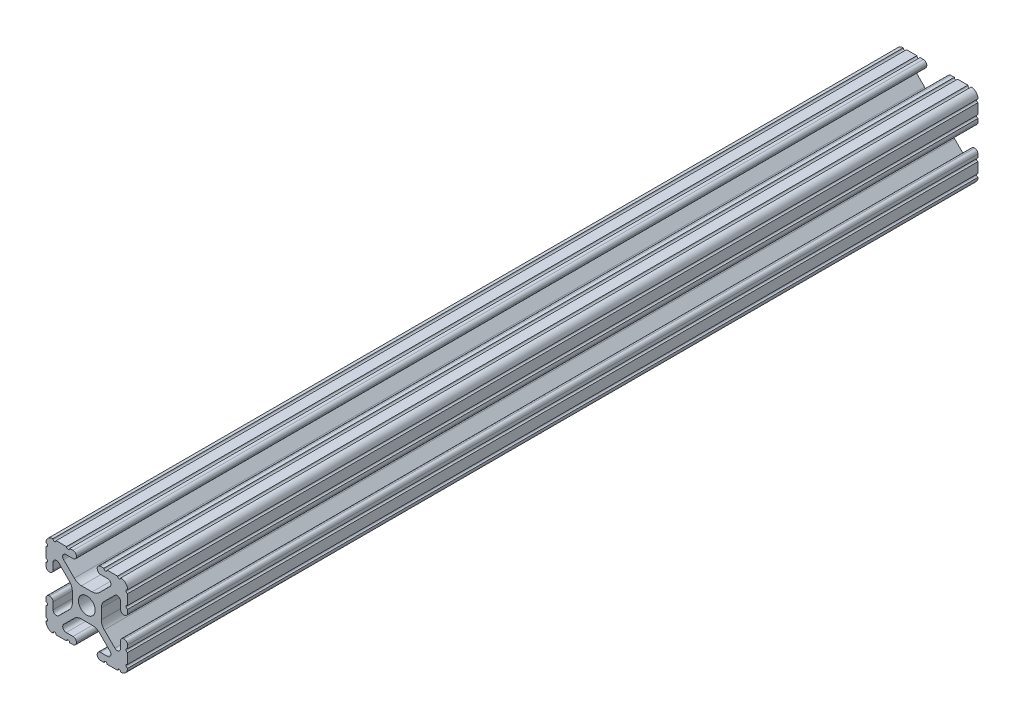
SolidWorks part; units mm, degrees
ref_plane "Front" through (0, 0, 0) normal (0, 0, 1) x (1, 0, 0)
ref_plane "Top" through (0, 0, 0) normal (0, 1, 0) x (1, 0, 0)
ref_plane "Right" through (0, 0, 0) normal (1, 0, 0) x (0, 0, -1)
sketch "Sketch1" plane through (0, 0, 0) normal (0, 0, 1) x (1, 0, 0)
  line L0 (-7.5107, 9.4563) -> (7.5107, 9.4563) construction
  line L1 (-7.4968, -9.4098) -> (7.4968, -9.4098) construction
  line L88 (-7.1797, -8.6452) -> (-3.9523, -5.4237)
  line L89 (-1.7093, -4.4958) -> (1.7093, -4.4958)
  line L90 (3.9523, -5.4237) -> (7.1797, -8.6452)
  line L91 (6.4164, -10.4902) -> (4.2875, -10.4902)
  line L92 (3.2385, -11.5392) -> (3.2385, -11.651)
  line L93 (4.2875, -12.7) -> (5.3171, -12.7)
  line L94 (6.3331, -12.7) -> (9.5504, -12.7)
  line L95 (12.7, -9.5504) -> (12.7, -6.3331)
  line L96 (12.7, -5.3171) -> (12.7, -4.2875)
  line L97 (11.651, -3.2385) -> (11.5392, -3.2385)
  line L98 (10.4902, -4.2875) -> (10.4902, -6.4021)
  line L99 (8.7371, -7.1294) -> (5.441, -3.8408)
  line L100 (4.5085, -1.5932) -> (4.5085, 1.5932)
  line L101 (5.441, 3.8408) -> (8.7371, 7.1294)
  line L102 (10.4902, 6.4021) -> (10.4902, 4.2875)
  line L103 (11.5392, 3.2385) -> (11.651, 3.2385)
  line L104 (12.7, 4.2875) -> (12.7, 5.3171)
  line L105 (12.7, 6.3331) -> (12.7, 9.5504)
  line L106 (9.5504, 12.7) -> (6.3331, 12.7)
  line L107 (5.3171, 12.7) -> (4.2875, 12.7)
  line L108 (3.2385, 11.651) -> (3.2385, 11.5392)
  line L109 (4.2875, 10.4902) -> (6.4768, 10.4902)
  line L110 (7.207, 8.7244) -> (3.8983, 5.4232)
  line L111 (1.6558, 4.4958) -> (-1.6558, 4.4958)
  line L112 (-3.8983, 5.4232) -> (-7.207, 8.7244)
  line L113 (-6.4768, 10.4902) -> (-4.2875, 10.4902)
  line L114 (-3.2385, 11.5392) -> (-3.2385, 11.651)
  line L115 (-4.2875, 12.7) -> (-5.3171, 12.7)
  line L116 (-6.3331, 12.7) -> (-9.5504, 12.7)
  line L117 (-12.7, 9.5504) -> (-12.7, 6.3331)
  line L118 (-12.7, 5.3171) -> (-12.7, 4.2875)
  line L119 (-11.651, 3.2385) -> (-11.5392, 3.2385)
  line L120 (-10.4902, 4.2875) -> (-10.4902, 6.4021)
  line L121 (-8.7371, 7.1294) -> (-5.441, 3.8408)
  line L122 (-4.5085, 1.5932) -> (-4.5085, -1.5932)
  line L123 (-5.441, -3.8408) -> (-8.7371, -7.1294)
  line L124 (-10.4902, -6.4021) -> (-10.4902, -4.2875)
  line L125 (-11.5392, -3.2385) -> (-11.651, -3.2385)
  line L126 (-12.7, -4.2875) -> (-12.7, -5.3171)
  line L127 (-12.7, -6.3331) -> (-12.7, -9.5504)
  line L128 (-9.5504, -12.7) -> (-6.3331, -12.7)
  line L129 (-5.3171, -12.7) -> (-4.2875, -12.7)
  line L130 (-3.2385, -11.651) -> (-3.2385, -11.5392)
  line L131 (-4.2875, -10.4902) -> (-6.4164, -10.4902)
  circle A1 centre (0, 0) radius 2.6035
  arc A104 (-7.1797, -8.6452) -> (-6.4164, -10.4902) centre (-6.4164, -9.4098) ccw
  arc A105 (-1.7093, -4.4958) -> (-3.9523, -5.4237) centre (-1.7093, -7.6708) ccw
  arc A106 (3.9523, -5.4237) -> (1.7093, -4.4958) centre (1.7093, -7.6708) ccw
  arc A107 (6.4164, -10.4902) -> (7.1797, -8.6452) centre (6.4164, -9.4098) ccw
  arc A108 (4.2875, -10.4902) -> (3.2385, -11.5392) centre (4.2875, -11.5392) ccw
  arc A109 (3.2385, -11.651) -> (4.2875, -12.7) centre (4.2875, -11.651) ccw
  arc A110 (6.3331, -12.7) -> (5.3171, -12.7) centre (5.8251, -12.7) ccw
  arc A111 (10.5664, -12.6998) -> (9.5504, -12.7) centre (10.0584, -12.7) ccw
  arc A112 (10.5664, -12.6998) -> (12.6998, -10.5664) centre (10.5918, -10.5918) ccw
  arc A113 (12.7, -9.5504) -> (12.6998, -10.5664) centre (12.7, -10.0584) ccw
  arc A114 (12.7, -5.3171) -> (12.7, -6.3331) centre (12.7, -5.8251) ccw
  arc A115 (12.7, -4.2875) -> (11.651, -3.2385) centre (11.651, -4.2875) ccw
  arc A116 (11.5392, -3.2385) -> (10.4902, -4.2875) centre (11.5392, -4.2875) ccw
  arc A117 (8.7371, -7.1294) -> (10.4902, -6.4021) centre (9.4628, -6.4021) ccw
  arc A118 (4.5085, -1.5932) -> (5.441, -3.8408) centre (7.6835, -1.5932) ccw
  arc A119 (5.441, 3.8408) -> (4.5085, 1.5932) centre (7.6835, 1.5932) ccw
  arc A120 (10.4902, 6.4021) -> (8.7371, 7.1294) centre (9.4628, 6.4021) ccw
  arc A121 (10.4902, 4.2875) -> (11.5392, 3.2385) centre (11.5392, 4.2875) ccw
  arc A122 (11.651, 3.2385) -> (12.7, 4.2875) centre (11.651, 4.2875) ccw
  arc A123 (12.7, 6.3331) -> (12.7, 5.3171) centre (12.7, 5.8251) ccw
  arc A124 (12.6998, 10.5664) -> (12.7, 9.5504) centre (12.7, 10.0584) ccw
  arc A125 (12.6998, 10.5664) -> (10.5664, 12.6998) centre (10.5918, 10.5918) ccw
  arc A126 (9.5504, 12.7) -> (10.5664, 12.6998) centre (10.0584, 12.7) ccw
  arc A127 (5.3171, 12.7) -> (6.3331, 12.7) centre (5.8251, 12.7) ccw
  arc A128 (4.2875, 12.7) -> (3.2385, 11.651) centre (4.2875, 11.651) ccw
  arc A129 (3.2385, 11.5392) -> (4.2875, 10.4902) centre (4.2875, 11.5392) ccw
  arc A130 (7.207, 8.7244) -> (6.4768, 10.4902) centre (6.4768, 9.4563) ccw
  arc A131 (1.6558, 4.4958) -> (3.8983, 5.4232) centre (1.6558, 7.6708) ccw
  arc A132 (-3.8983, 5.4232) -> (-1.6558, 4.4958) centre (-1.6558, 7.6708) ccw
  arc A133 (-6.4768, 10.4902) -> (-7.207, 8.7244) centre (-6.4768, 9.4563) ccw
  arc A134 (-4.2875, 10.4902) -> (-3.2385, 11.5392) centre (-4.2875, 11.5392) ccw
  arc A135 (-3.2385, 11.651) -> (-4.2875, 12.7) centre (-4.2875, 11.651) ccw
  arc A136 (-6.3331, 12.7) -> (-5.3171, 12.7) centre (-5.8251, 12.7) ccw
  arc A137 (-10.5664, 12.6998) -> (-9.5504, 12.7) centre (-10.0584, 12.7) ccw
  arc A138 (-10.5664, 12.6998) -> (-12.6998, 10.5664) centre (-10.5918, 10.5918) ccw
  arc A139 (-12.7, 9.5504) -> (-12.6998, 10.5664) centre (-12.7, 10.0584) ccw
  arc A140 (-12.7, 5.3171) -> (-12.7, 6.3331) centre (-12.7, 5.8251) ccw
  arc A141 (-12.7, 4.2875) -> (-11.651, 3.2385) centre (-11.651, 4.2875) ccw
  arc A142 (-11.5392, 3.2385) -> (-10.4902, 4.2875) centre (-11.5392, 4.2875) ccw
  arc A143 (-8.7371, 7.1294) -> (-10.4902, 6.4021) centre (-9.4628, 6.4021) ccw
  arc A144 (-4.5085, 1.5932) -> (-5.441, 3.8408) centre (-7.6835, 1.5932) ccw
  arc A145 (-5.441, -3.8408) -> (-4.5085, -1.5932) centre (-7.6835, -1.5932) ccw
  arc A146 (-10.4902, -6.4021) -> (-8.7371, -7.1294) centre (-9.4628, -6.4021) ccw
  arc A147 (-10.4902, -4.2875) -> (-11.5392, -3.2385) centre (-11.5392, -4.2875) ccw
  arc A148 (-11.651, -3.2385) -> (-12.7, -4.2875) centre (-11.651, -4.2875) ccw
  arc A149 (-12.7, -6.3331) -> (-12.7, -5.3171) centre (-12.7, -5.8251) ccw
  arc A150 (-12.6998, -10.5664) -> (-12.7, -9.5504) centre (-12.7, -10.0584) ccw
  arc A151 (-12.6998, -10.5664) -> (-10.5664, -12.6998) centre (-10.5918, -10.5918) ccw
  arc A152 (-9.5504, -12.7) -> (-10.5664, -12.6998) centre (-10.0584, -12.7) ccw
  arc A153 (-5.3171, -12.7) -> (-6.3331, -12.7) centre (-5.8251, -12.7) ccw
  arc A154 (-4.2875, -12.7) -> (-3.2385, -11.651) centre (-4.2875, -11.651) ccw
  arc A155 (-3.2385, -11.5392) -> (-4.2875, -10.4902) centre (-4.2875, -11.5392) ccw
extrude "Boss-Extrude1" add sketch "Sketch1" along normal mid plane 914.4
sketch "Sketch3" plane through (-12.7, 0, 0) normal (-1, 0, 0) x (0, 0, 1)
  line L0 (-203.2, -25.4) -> (-203.2, 21.1581) construction
  line L1 (-203.2, -27.5528) -> (-203.2, 21.1581)
  line L2 (-203.2, 21.1581) -> (-461.0909, 21.1581)
  line L3 (-461.0909, 21.1581) -> (-461.0909, -25.4)
  line L4 (-461.0909, -25.4) -> (-203.2, -27.5528)
extrude "Cut-Extrude2" cut sketch "Sketch3" against normal blind 26.924 and the other way blind 4.318
sketch "Sketch5" plane through (12.7, 0, 0) normal (1, 0, 0) x (0, 0, -1)
  line L0 (-192.5442, -19.3511) -> (-192.5442, 300.5827) construction
  line L1 (-192.5442, -19.3511) -> (208.319, -19.3511)
  line L2 (208.319, -19.3511) -> (208.319, 23.9761)
  line L3 (208.319, 23.9761) -> (-192.5442, 23.9761)
  line L4 (-192.5442, 23.9761) -> (-192.5442, -19.3511)
  point P5 (-192.5442, 300.5827)
extrude "Cut-Extrude3" cut sketch "Sketch5" against normal through all
